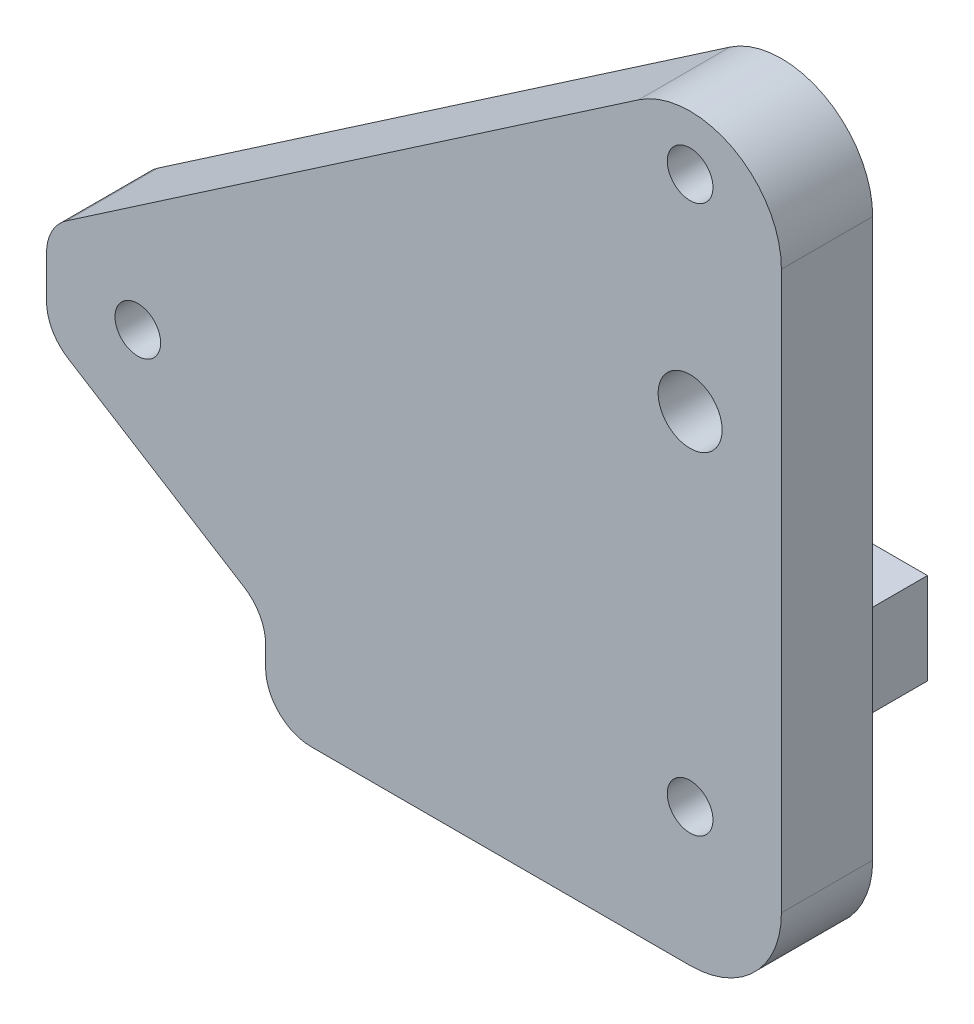
SolidWorks part; units mm, degrees
ref_plane "Front Plane" through (0, 0, 0) normal (0, 0, 1) x (1, 0, 0)
ref_plane "Top Plane" through (0, 0, 0) normal (0, 1, 0) x (1, 0, 0)
ref_plane "Right Plane" through (0, 0, 0) normal (1, 0, 0) x (0, 0, -1)
sketch "Sketch1" plane through (0, 0, 0) normal (0, 0, 1) x (1, 0, 0)
  line L1 (-15.6413, 26.7475) -> (-78.3207, -16.0769)
  line L2 (-80.5, -20.2053) -> (-80.5, -24.7947)
  line L7 (0, 18.4906) -> (0, -42.5659)
  line L9 (-10, 0) -> (-73, 0) construction
  line L10 (-41.5, 0) -> (-41.5, 23.034) construction
  line L11 (-10, -52.5659) -> (-51.5, -52.5659)
  line L12 (-56.5, -47.5659) -> (-56.5, -45.3371)
  line L13 (-58.85, -41.0971) -> (-78.15, -29.0347)
  line L15 (-56.5, -52.5659) -> (-26.5, -52.5659)
  line L16 (-56.5, -52.5659) -> (-56.5, -42.5659)
  line L17 (-56.5, -42.5659) -> (-26.5, -42.5659)
  line L18 (-26.5, -52.5659) -> (-26.5, -42.5659)
  circle A0 centre (-10, 0) radius 3.5
  circle A3 centre (-10, 22.5) radius 2.5
  circle A5 centre (-70.5, -22.5) radius 2.5
  circle A6 centre (-10, -37.5) radius 2.5
  arc A7 (0, -42.5659) -> (-10, -52.5659) centre (-10, -42.5659) cw
  arc A8 (0, 18.4906) -> (-15.6413, 26.7475) centre (-10, 18.4906) ccw
  arc A9 (-80.5, -24.7947) -> (-78.15, -29.0347) centre (-75.5, -24.7947) ccw
  arc A10 (-80.5, -20.2053) -> (-78.3207, -16.0769) centre (-75.5, -20.2053) cw
  arc A11 (-51.5, -52.5659) -> (-56.5, -47.5659) centre (-51.5, -47.5659) cw
  arc A12 (-56.5, -45.3371) -> (-58.85, -41.0971) centre (-61.5, -45.3371) ccw
  point P3 (-41.5, -42.5659)
  point P10 (-80.5, -22.5)
  point P36 (0, -52.5659)
  point P39 (0, 37.4341)
  point P42 (-80.5, -27.5659)
  point P46 (-80.5, -17.5659)
  dimension "D1" = 7
  dimension "D8" = 90
  dimension "D9" = 10
  dimension "D10" = 5
  dimension "D12" = 22.5
  dimension "D14" = 5
  dimension "D17" = 5
  dimension "D22" = 10
  dimension "D23" = 5
  dimension "D13" = 60.5
  dimension "D6" = 0
  dimension "D24" = 5
  dimension "D25" = 5
  dimension "D2" = 10
  dimension "D3" = 30
  dimension "D4" = 0
  dimension "D5" = 10
  dimension "D7" = 0
  dimension "D11" = 22.5
  dimension "D15" = 56.5
  dimension "D16" = 60
  dimension "D18" = 24
  dimension "D19" = 80.5
  dimension "D20" = 15
  dimension "D21" = 55
extrude "Boss-Extrude1" add sketch "Sketch1" along normal blind 10 contours L13 A9 L2 A10 L1 A8 L7 A7 L11 A11 L12 A12 | A5 | A6 | A0 | A3
sketch "Sketch3" plane through (0, 0, 10) normal (0, 0, 1) x (1, 0, 0)
  line L0 (-70.5, -22.5) -> (-70.5, 9.7465) construction
  line L1 (-10, 0) -> (-70.5, 0) construction
  line L2 (-40.25, 0) -> (-40.25, -57.641) construction
  line L3 (-10, -52.5659) -> (-51.5, -52.5659) construction
  line L4 (-24, -52.5659) -> (-51.5, -52.5659)
  line L5 (-24, -52.5659) -> (-24, -42.5659)
  line L6 (-24, -42.5659) -> (-56.5, -42.5659)
  line L7 (-56.5, -47.5659) -> (-56.5, -42.5659)
  arc A0 (-56.5, -47.5659) -> (-51.5, -52.5659) centre (-51.5, -47.5659) ccw construction
  arc A1 (-56.5, -47.5659) -> (-51.5, -52.5659) centre (-51.5, -47.5659) ccw
  point P16 (-40.25, -42.5659)
  dimension "D1" = 10
  dimension "D3" = 0
extrude "Boss-Extrude2" add sketch "Sketch3" against normal blind 30 from offset 10 offset against normal yes
sketch "Sketch4" plane through (0, -42.5659, 0) normal (0, 1, 0) x (1, 0, 0)
  line L0 (-24, 30) -> (-56.5, 30) construction
  line L1 (-24, 30) -> (-56.5, 30)
  circle A0 centre (-40.25, 15) radius 5.25
  circle A1 centre (-32.25, 15) radius 1.75
  circle A2 centre (-40.25, 23) radius 1.75
  circle A3 centre (-48.25, 15) radius 1.75
  circle A4 centre (-40.25, 7) radius 1.75
  point P13 (-40.25, 30)
  dimension "D4" = 10.5
  dimension "D5" = 3.5
  dimension "D6" = 3.5
  dimension "D7" = 3.5
  dimension "D8" = 3.5
  dimension "D1" = 15
  dimension "D2" = 16
  dimension "D3" = 16
  dimension "D9" = 8
  dimension "D10" = 8
extrude "Cut-Extrude1" cut sketch "Sketch4" against normal through all contours A0 | A2 | A3 | A1 | A4
